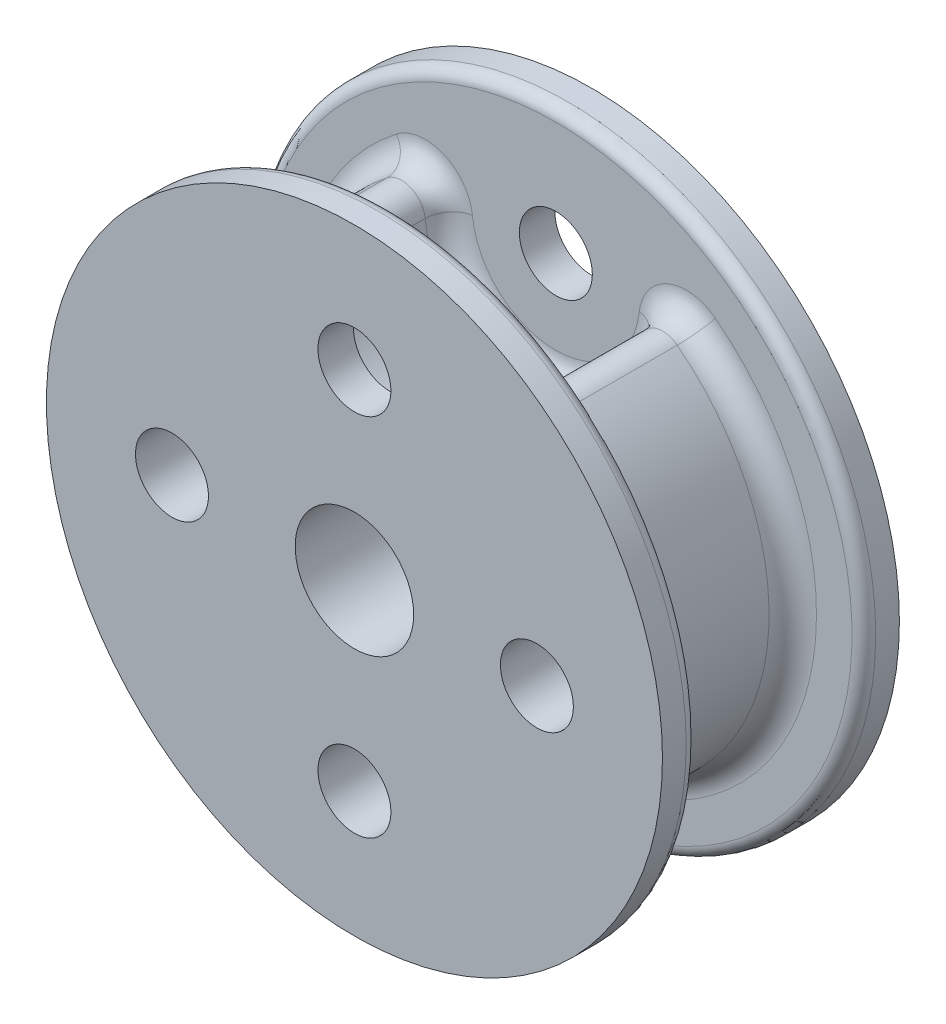
SolidWorks part; units mm, degrees
ref_plane "Front Plane" through (0, 0, 0) normal (0, 0, 1) x (1, 0, 0)
ref_plane "Top Plane" through (0, 0, 0) normal (0, 1, 0) x (1, 0, 0)
ref_plane "Right Plane" through (0, 0, 0) normal (1, 0, 0) x (0, 0, -1)
sketch "Sketch2" plane through (0, 0, 0) normal (0, 0, 1) x (1, 0, 0)
  circle A0 centre (0, 0) radius 12.7
  circle A1 centre (0, 9.779) radius 1.9558
  circle A3 centre (9.779, 0) radius 1.9558
  circle A4 centre (0, -9.779) radius 1.9558
  circle A5 centre (-9.779, 0) radius 1.9558
  arc A6 (-5.5224, 11.4365) -> (5.5224, 11.4365) centre (0, 9.779) ccw
  circle A7 centre (0, 0) radius 3.175
  point P14 (0, 0)
  dimension "D1" = 3.9116
  dimension "D2" = 4
  dimension "D4" = 25.4
  dimension "D5" = 3.81
  dimension "D6" = 6.35
  dimension "D3" = 9.779
extrude "Boss-Extrude3" add sketch "Sketch2" along normal mid plane 8.89 contours A6 A0 A7 A5 A4 A3
sketch "Sketch3" plane through (0, 0, 4.445) normal (0, 0, 1) x (1, 0, 0)
  circle A0 centre (0, 0) radius 16.51
  circle A1 centre (0, -9.779) radius 1.9558 construction
  circle A2 centre (9.779, 0) radius 1.9558 construction
  circle A3 centre (0, 0) radius 3.175 construction
  circle A4 centre (-9.779, 0) radius 1.9558 construction
  circle A5 centre (0, -9.779) radius 1.9558
  circle A6 centre (9.779, 0) radius 1.9558
  circle A7 centre (0, 0) radius 3.175
  circle A8 centre (-9.779, 0) radius 1.9558
  circle A9 centre (0, 9.779) radius 1.9558
  dimension "D1" = 33.02
  dimension "D2" = 3.9116
  dimension "D3" = 9.779
extrude "Boss-Extrude4" add sketch "Sketch3" along normal blind 1.905 contours A0
mirror "Mirror1" about plane through (0, 0, 0) normal (0, 0, 1) of "Boss-Extrude4"
fillet "Fillet1" radius 1.27 6 edges at (0, 4.0132, 4.445) (0, 4.0132, -4.445) (-5.5224, 11.4365, 0) (5.5224, 11.4365, 0) (0, -12.7, -4.445) (0, -12.7, 4.445)
fillet "Fillet3" radius 0.635 2 edges at (16.51, 0, 4.445) (16.51, 0, -4.445)
